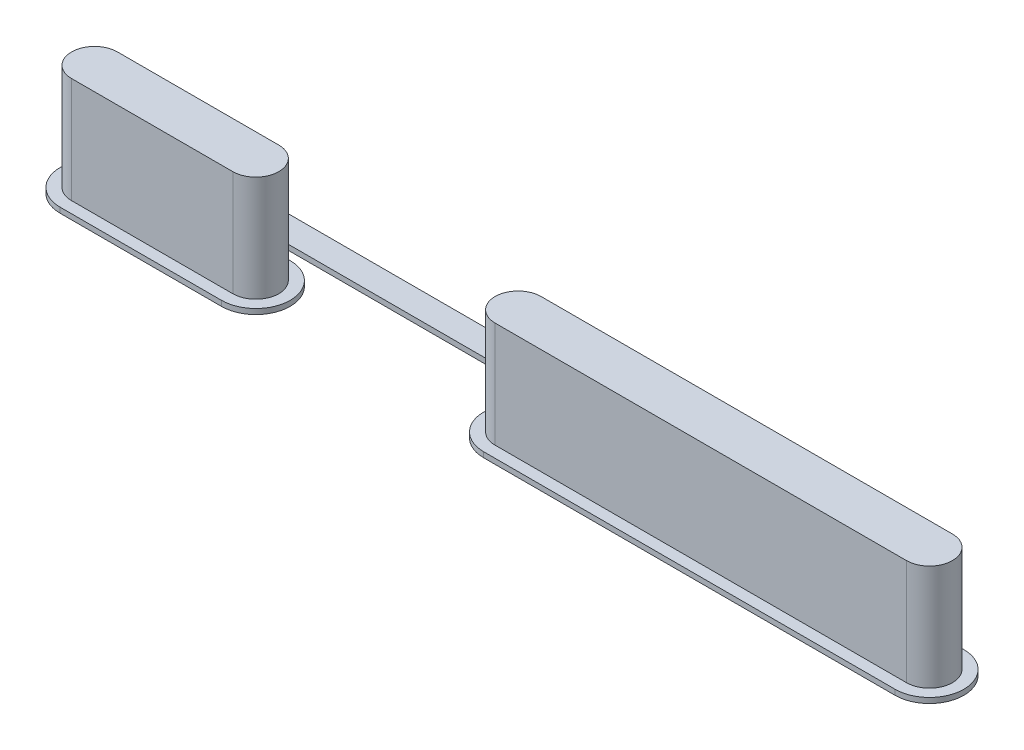
SolidWorks part; units mm, degrees
ref_plane "Front Plane" through (0, 0, 0) normal (0, 0, 1) x (1, 0, 0)
ref_plane "Top Plane" through (0, 0, 0) normal (0, 1, 0) x (1, 0, 0)
ref_plane "Right Plane" through (0, 0, 0) normal (1, 0, 0) x (0, 0, -1)
sketch "Sketch1" plane through (0, 0, 0) normal (0, 1, 0) x (1, 0, 0)
  line L0 (-3.8735, 0) -> (3.8735, 0) construction
  line L1 (-3.8735, 1.1049) -> (3.8735, 1.1049)
  line L2 (-3.8735, -1.1049) -> (3.8735, -1.1049)
  line L3 (16.4719, 0) -> (36.2331, 0) construction
  line L4 (16.4719, 1.1049) -> (36.2331, 1.1049)
  line L5 (16.4719, -1.1049) -> (36.2331, -1.1049)
  arc A0 (-3.8735, 1.1049) -> (-3.8735, -1.1049) centre (-3.8735, 0) ccw
  arc A1 (3.8735, -1.1049) -> (3.8735, 1.1049) centre (3.8735, 0) ccw
  arc A2 (16.4719, 1.1049) -> (16.4719, -1.1049) centre (16.4719, 0) ccw
  arc A3 (36.2331, -1.1049) -> (36.2331, 1.1049) centre (36.2331, 0) ccw
  point P2 (0, 0)
  point P10 (26.3525, 0)
  dimension "D1" = 9.9568
  dimension "D2" = 2.2098
  dimension "D3" = 26.3525
  dimension "D4" = 19.7612
extrude "Boss-Extrude1" add sketch "Sketch1" along normal blind 5.08
sketch "Sketch3" plane through (0, 0, 0) normal (0, 1, 0) x (1, 0, 0)
  line L0 (-3.8735, 0) -> (3.8735, 0) construction
  line L1 (-3.8735, 1.651) -> (3.8735, 1.651)
  line L2 (-3.8735, -1.651) -> (3.8735, -1.651)
  line L3 (16.4719, 0) -> (36.2331, 0) construction
  line L4 (16.4719, 1.651) -> (36.2331, 1.651)
  line L5 (16.4719, -1.651) -> (36.2331, -1.651)
  arc A0 (-3.8735, 1.651) -> (-3.8735, -1.651) centre (-3.8735, 0) ccw
  arc A1 (3.8735, -1.651) -> (3.8735, 1.651) centre (3.8735, 0) ccw
  arc A2 (16.4719, 1.651) -> (16.4719, -1.651) centre (16.4719, 0) ccw
  arc A3 (36.2331, -1.651) -> (36.2331, 1.651) centre (36.2331, 0) ccw
  point P2 (0, 0)
  point P13 (26.3525, 0)
  dimension "D1" = 3.302
extrude "Boss-Extrude2" add sketch "Sketch3" against normal blind 0.254
sketch "Sketch4" plane through (0, 0, 0) normal (0, 1, 0) x (1, 0, 0)
  line L0 (0, 1.651) -> (0, 2.032)
  line L1 (3.8735, 1.651) -> (-3.8735, 1.651) construction
  line L2 (0.889, 2.921) -> (25.4635, 2.921)
  line L3 (26.3525, 2.032) -> (26.3525, 1.651)
  line L4 (36.2331, 1.651) -> (16.4719, 1.651) construction
  arc A0 (25.4635, 2.921) -> (26.3525, 2.032) centre (25.4635, 2.032) cw
  arc A1 (0, 2.032) -> (0.889, 2.921) centre (0.889, 2.032) cw
  dimension "D1" = 0.889
  dimension "D2" = 0.381
extrude "Extrude-Thin1" add sketch "Sketch4" against normal up to surface (0.254 mm away) thin up to face at (0, -0.254, 0) thin type mid plane wall 1.27
fillet "Fillet1" radius 0.254 4 edges at (-0.635, -0.127, -1.651) (26.9875, -0.127, -1.651) (25.7175, -0.127, -1.651) (0.635, -0.127, -1.651)
